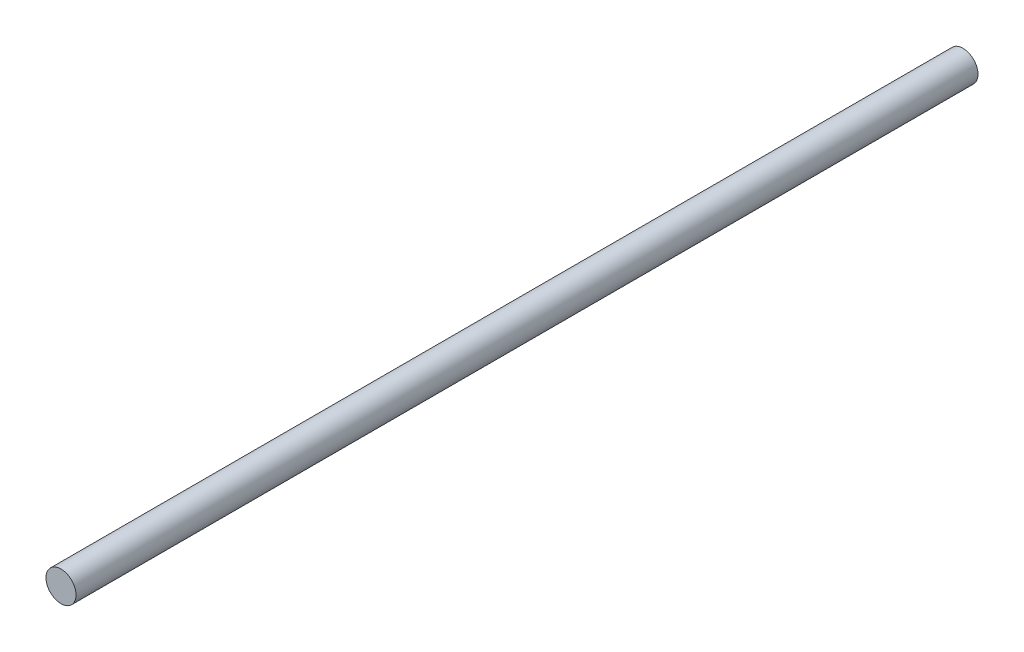
SolidWorks part; units mm, degrees
ref_plane "Ön Düzlem" through (0, 0, 0) normal (0, 0, 1) x (1, 0, 0)
ref_plane "Üst Düzlem" through (0, 0, 0) normal (0, 1, 0) x (1, 0, 0)
ref_plane "Sağ Düzlem" through (0, 0, 0) normal (1, 0, 0) x (0, 0, -1)
sketch "Çizim1" plane through (0, 0, 0) normal (0, 0, 1) x (1, 0, 0)
  circle A0 centre (0, 0) radius 4
  dimension "D1" = 8
extrude "Yükseklik-Ekstrüzyon1" add sketch "Çizim1" along normal blind 240
